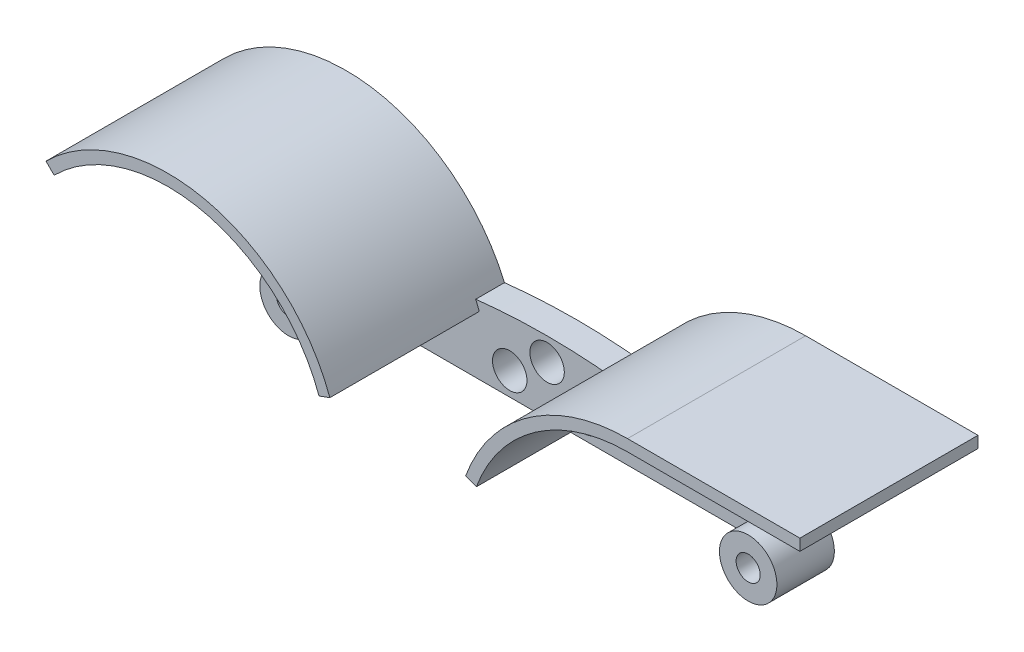
SolidWorks part; units mm, degrees
ref_plane "Front Plane" through (0, 0, 0) normal (0, 0, 1) x (1, 0, 0)
ref_plane "Top Plane" through (0, 0, 0) normal (0, 1, 0) x (1, 0, 0)
ref_plane "Right Plane" through (0, 0, 0) normal (1, 0, 0) x (0, 0, -1)
sketch "Sketch2" plane through (0, 0, 0) normal (0, 0, 1) x (1, 0, 0)
  line L0 (-35, -12.5) -> (35, -12.5)
  line L1 (-40, -12.5) -> (40, -12.5) construction
  line L2 (-40, -12.5) -> (-40, 12.5) construction
  line L3 (-40, 12.5) -> (40, 12.5) construction
  line L4 (40, -12.5) -> (40, 12.5) construction
  line L5 (-40, -12.5) -> (40, 12.5) construction
  line L6 (-40, 12.5) -> (40, -12.5) construction
  arc A2 (-40, -7.5) -> (-35, -12.5) centre (-40, -12.5) ccw
  arc A3 (35, -12.5) -> (40, -7.5) centre (40, -12.5) ccw
  arc A4 (-40, -7.5) -> (40, -7.5) centre (0, -110.4167) cw
  point P0 (0, 0)
  dimension "D5" = 10
  dimension "D6" = 10
  dimension "D1" = 80
  dimension "D2" = 25
extrude "Boss-Extrude1" add sketch "Sketch2" along normal blind 5
sketch "Sketch3" plane through (0, 0, 5) normal (0, 0, 1) x (1, 0, 0)
  line L0 (-45, -12.5) -> (-35, -12.5) construction
  line L1 (35, -12.5) -> (45, -12.5) construction
  arc A0 (-40, -7.5) -> (-35, -12.5) centre (-40, -12.5) ccw construction
  arc A1 (35, -12.5) -> (40, -7.5) centre (40, -12.5) ccw construction
  circle A2 centre (-40, -12.5) radius 5
  circle A3 centre (40, -12.5) radius 5
extrude "Boss-Extrude2" add sketch "Sketch3" along normal blind 5
sketch "Sketch4" plane through (0, 0, 0) normal (0, 0, -1) x (-1, 0, 0)
  line L0 (-35, -12.5) -> (-45, -12.5) construction
  line L1 (35, -12.5) -> (45, -12.5) construction
  line L2 (-70, 17.5) -> (-70, 15.5)
  line L3 (40, -12.5) -> (61.2132, 8.7132) construction
  line L4 (-40, -12.5) -> (-40, 17.5) construction
  line L5 (35, -12.5) -> (-35, -12.5) construction
  line L6 (-40, 17.5) -> (-70, 17.5)
  line L7 (-70, 15.5) -> (-40, -12.5)
  line L8 (61.2132, 8.7132) -> (40, -12.5)
  line L9 (40, -12.5) -> (10, -12.5)
  line L10 (-10, -12.5) -> (-40, -12.5)
  arc A0 (-40, -7.5) -> (-35, -12.5) centre (-40, -12.5) ccw construction
  arc A1 (35, -12.5) -> (40, -7.5) centre (40, -12.5) ccw construction
  circle A2 centre (-40, -12.5) radius 28 construction
  circle A3 centre (40, -12.5) radius 28 construction
  circle A4 centre (-40, -12.5) radius 30 construction
  circle A5 centre (40, -12.5) radius 30 construction
  arc A6 (-10, -12.5) -> (-40, 17.5) centre (-40, -12.5) ccw
  arc A7 (10, -12.5) -> (61.2132, 8.7132) centre (40, -12.5) cw
  arc M1 (35, -12.5) -> (40, -7.5) centre (40, -12.5) ccw
  arc M2 (40, -7.5) -> (-40, -7.5) centre (0, -110.4167) ccw
  arc M3 (-40, -7.5) -> (-35, -12.5) centre (-40, -12.5) ccw
  dimension "D1" = 56
  dimension "D2" = 56
  dimension "D5" = 45
  dimension "D6" = 30
  dimension "D3" = 2
  dimension "D4" = 2
  dimension "D7" = 2
extrude "Boss-Extrude3" add sketch "Sketch4" against normal blind 2 contours A6 L6 L2 L7 M2 M3 | A7 L8 M2 M1
sketch "Sketch5" plane through (0, 0, 2) normal (0, 0, 1) x (1, 0, 0)
  line L0 (-35, -12.5) -> (-45, -12.5) construction
  line L1 (35, -12.5) -> (45, -12.5) construction
  line L2 (-61.2132, 8.7132) -> (-43.5355, -8.9645) construction
  line L3 (-40, -12.5) -> (-11.8092, -2.2394) construction
  line L4 (-59.799, 7.299) -> (-61.2132, 8.7132)
  line L5 (40, -12.5) -> (11.8092, -2.2394) construction
  line L6 (-35, -12.5) -> (35, -12.5) construction
  line L7 (-11.8092, -2.2394) -> (-13.6886, -2.9234)
  line L8 (40, 17.5) -> (70, 17.5)
  line L9 (70, 17.5) -> (70, 15.5)
  line L10 (70, 15.5) -> (40, 15.5)
  line L11 (13.6886, -2.9234) -> (11.8092, -2.2394)
  circle A0 centre (-40, -12.5) radius 5 construction
  circle A1 centre (40, -12.5) radius 5 construction
  arc A2 (40, -7.5) -> (35, -12.5) centre (40, -12.5) ccw construction
  circle A3 centre (-40, -12.5) radius 30 construction
  circle A4 centre (40, -12.5) radius 30 construction
  arc A5 (-12.4179, -0.7005) -> (-61.2132, 8.7132) centre (-40, -12.5) ccw construction
  arc A6 (40, 17.5) -> (12.4179, -0.7005) centre (40, -12.5) ccw construction
  circle A7 centre (-40, -12.5) radius 28 construction
  circle A8 centre (40, -12.5) radius 28 construction
  arc A9 (-61.2132, 8.7132) -> (-11.8092, -2.2394) centre (-40, -12.5) cw
  arc A10 (11.8092, -2.2394) -> (40, 17.5) centre (40, -12.5) cw
  arc A11 (-59.799, 7.299) -> (-13.6886, -2.9234) centre (-40, -12.5) cw
  arc A12 (13.6886, -2.9234) -> (40, 15.5) centre (40, -12.5) cw
  dimension "D1" = 2
  dimension "D2" = 2
  dimension "D3" = 20
  dimension "D4" = 20
extrude "Boss-Extrude5" add sketch "Sketch5" along normal blind 29
sketch "Sketch6" plane through (0, 0, 10) normal (0, 0, 1) x (1, 0, 0)
  line L0 (-35, -12.5) -> (-45, -12.5) construction
  line L1 (35, -12.5) -> (45, -12.5) construction
  line L2 (-35, -12.5) -> (35, -12.5) construction
  line L3 (0, 0) -> (0, -12.5) construction
  circle A0 centre (-40, -12.5) radius 2.1
  circle A1 centre (40, -12.5) radius 2.1
  circle A2 centre (0, -4) radius 3
  arc A3 (12.4179, -0.7005) -> (-12.4179, -0.7005) centre (0, -110.4167) ccw construction
  circle A4 centre (-6.5, -8.5) radius 3
  circle A5 centre (6.5, -8.5) radius 3
  dimension "D1" = 4.2
  dimension "D2" = 4.2
  dimension "D3" = 6
  dimension "D5" = 6
  dimension "D4" = 8.5
  dimension "D6" = 4
  dimension "D7" = 6.5
extrude "Cut-Extrude1" cut sketch "Sketch6" against normal through all
